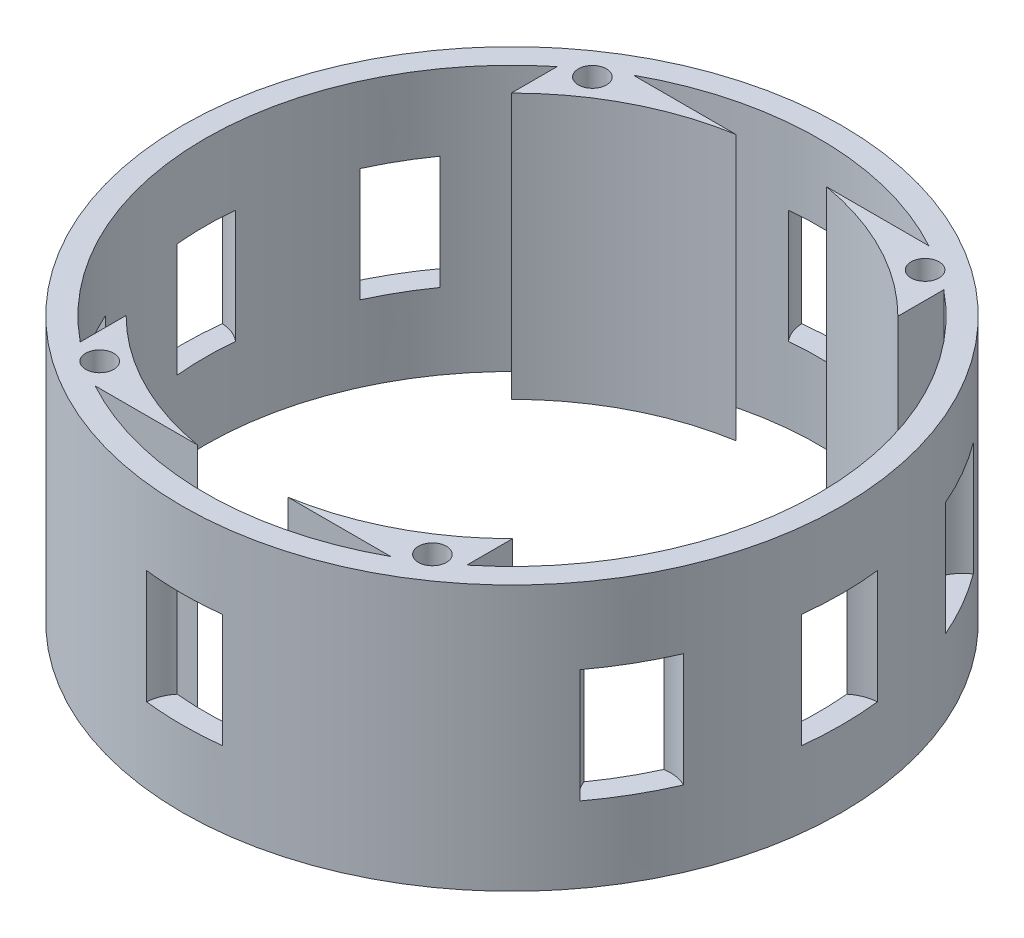
SolidWorks part; units mm, degrees
ref_plane "Front Plane" through (0, 0, 0) normal (0, 0, 1) x (1, 0, 0)
ref_plane "Top Plane" through (0, 0, 0) normal (0, 1, 0) x (1, 0, 0)
ref_plane "Right Plane" through (0, 0, 0) normal (1, 0, 0) x (0, 0, -1)
sketch "Sketch1" plane through (0, 0, 0) normal (0, 1, 0) x (1, 0, 0)
  line L0 (-25.5, 31.4643) -> (-25.5, 25.4116)
  line L5 (-25.5, 35.5) -> (25.5, -35.5) construction
  line L6 (-25.5, -35.5) -> (25.5, 35.5) construction
  line L7 (-19.4936, 35.5) -> (-5.9791, 35.5)
  line L8 (5.9791, 35.5) -> (19.4936, 35.5)
  line L9 (-25.5, -25.4116) -> (-25.5, -31.4643)
  line L10 (5.9791, -35.5) -> (19.4936, -35.5)
  line L11 (25.5, 31.4643) -> (25.5, 25.4116)
  line L12 (25.5, -25.4116) -> (25.5, -31.4643)
  line L13 (-19.4936, -35.5) -> (-5.9791, -35.5)
  circle A0 centre (0, 0) radius 40.5
  circle A1 centre (0, 0) radius 43.5
  arc A2 (-25.5, -25.4116) -> (-5.9791, -35.5) centre (0, 0) ccw
  arc A3 (25.5, 25.4116) -> (5.9791, 35.5) centre (0, 0) ccw
  arc A4 (5.9791, -35.5) -> (25.5, -25.4116) centre (0, 0) ccw
  arc A5 (-5.9791, 35.5) -> (-25.5, 25.4116) centre (0, 0) ccw
  dimension "D1" = 81
  dimension "D2" = 87
  dimension "D5" = 72
  dimension "D3" = 71
  dimension "D4" = 51
extrude "Boss-Extrude1" add sketch "Sketch1" along normal blind 35 contours A1 A0 | A2 L9 A0 L13 | A4 L10 A0 L12 | A3 L11 A0 L8 | A5 L7 A0 L0
sketch "Sketch2" plane through (0, 35, 0) normal (0, 1, 0) x (1, 0, 0)
  line L1 (-25, 35) -> (25, 35)
  line L2 (-25, 35) -> (-25, -35)
  line L3 (-25, -35) -> (25, -35)
  line L4 (25, 35) -> (25, -35)
  line L5 (-25, 35) -> (25, -35) construction
  line L6 (-25, -35) -> (25, 35) construction
  circle A0 centre (-22, 32.6064) radius 1.85
  circle A1 centre (22, 32.5) radius 1.85
  circle A2 centre (22, -32.5) radius 1.85
  circle A3 centre (-22, -32.3936) radius 1.85
  point P0 (0, 0)
  dimension "D7" = 3.7
  dimension "D1" = 70
  dimension "D2" = 50
  dimension "D3" = 65
  dimension "D4" = 65
  dimension "D5" = 44
  dimension "D6" = 44
  dimension "D8" = 3
  dimension "D9" = 3
  dimension "D10" = 2.6064
  dimension "D11" = 2.5
extrude "Cut-Extrude1" cut sketch "Sketch2" against normal blind 15 contours A0 | A1 | A2 | A3
sketch "Sketch3" plane through (0, 0, 0) normal (0, 0, 1) x (1, 0, 0)
  line L0 (0, -2.1211) -> (0, 39.6886) construction
  line L1 (-43.5, 17.5) -> (43.5, 17.5) construction
  line L2 (-43.5, 35) -> (-43.5, 0) construction
  line L3 (43.5, 0) -> (43.5, 35) construction
sketch "Sketch5" plane through (0, 0, 0) normal (0, 1, 0) x (1, 0, 0)
  circle A0 centre (0, 0) radius 43.5 construction
  arc A1 (19.4936, 35.5) -> (-19.4936, 35.5) centre (0, 0) ccw construction
  arc A2 (4.9917, 43.2126) -> (-4.9917, 43.2126) centre (0, 0) ccw
  arc A3 (3.8552, 40.3161) -> (-3.8552, 40.3161) centre (0, 0) ccw
  arc A4 (3.8552, 40.3161) -> (4.9917, 43.2126) centre (0, 43.5) ccw
  arc A5 (-4.9917, 43.2126) -> (-3.8552, 40.3161) centre (0, 43.5) ccw
  arc A10 (36.8424, 16.8193) -> (32.9871, 23.4968) centre (0, 0) ccw
  arc A11 (34.9274, 25.9293) -> (32.9871, 23.4968) centre (37.6721, 21.75) ccw
  arc A12 (39.9191, 17.2834) -> (34.9274, 25.9293) centre (0, 0) ccw
  arc A13 (36.8424, 16.8193) -> (39.9191, 17.2834) centre (37.6721, 21.75) ccw
  arc A14 (40.3161, -3.8552) -> (40.3161, 3.8552) centre (0, 0) ccw
  arc A15 (43.2126, 4.9917) -> (40.3161, 3.8552) centre (43.5, 0) ccw
  arc A16 (43.2126, -4.9917) -> (43.2126, 4.9917) centre (0, 0) ccw
  arc A17 (40.3161, -3.8552) -> (43.2126, -4.9917) centre (43.5, 0) ccw
  arc A18 (32.9871, -23.4968) -> (36.8424, -16.8193) centre (0, 0) ccw
  arc A19 (39.9191, -17.2834) -> (36.8424, -16.8193) centre (37.6721, -21.75) ccw
  arc A20 (34.9274, -25.9293) -> (39.9191, -17.2834) centre (0, 0) ccw
  arc A21 (32.9871, -23.4968) -> (34.9274, -25.9293) centre (37.6721, -21.75) ccw
  arc A26 (-3.8552, -40.3161) -> (3.8552, -40.3161) centre (0, 0) ccw
  arc A27 (4.9917, -43.2126) -> (3.8552, -40.3161) centre (0, -43.5) ccw
  arc A28 (-4.9917, -43.2126) -> (4.9917, -43.2126) centre (0, 0) ccw
  arc A29 (-3.8552, -40.3161) -> (-4.9917, -43.2126) centre (0, -43.5) ccw
  arc A34 (-36.8424, -16.8193) -> (-32.9871, -23.4968) centre (0, 0) ccw
  arc A35 (-34.9274, -25.9293) -> (-32.9871, -23.4968) centre (-37.6721, -21.75) ccw
  arc A36 (-39.9191, -17.2834) -> (-34.9274, -25.9293) centre (0, 0) ccw
  arc A37 (-36.8424, -16.8193) -> (-39.9191, -17.2834) centre (-37.6721, -21.75) ccw
  arc A38 (-40.3161, 3.8552) -> (-40.3161, -3.8552) centre (0, 0) ccw
  arc A39 (-43.2126, -4.9917) -> (-40.3161, -3.8552) centre (-43.5, 0) ccw
  arc A40 (-43.2126, 4.9917) -> (-43.2126, -4.9917) centre (0, 0) ccw
  arc A41 (-40.3161, 3.8552) -> (-43.2126, 4.9917) centre (-43.5, 0) ccw
  arc A42 (-32.9871, 23.4968) -> (-36.8424, 16.8193) centre (0, 0) ccw
  arc A43 (-39.9191, 17.2834) -> (-36.8424, 16.8193) centre (-37.6721, 21.75) ccw
  arc A44 (-34.9274, 25.9293) -> (-39.9191, 17.2834) centre (0, 0) ccw
  arc A45 (-32.9871, 23.4968) -> (-34.9274, 25.9293) centre (-37.6721, 21.75) ccw
  arc A50 (25.9293, -34.9274) -> (23.4968, -32.9871) centre (21.75, -37.6721) ccw [skipped]
  arc A51 (17.2834, -39.9191) -> (25.9293, -34.9274) centre (0, 0) ccw [skipped]
  arc A52 (16.8193, -36.8424) -> (23.4968, -32.9871) centre (0, 0) ccw [skipped]
  arc A53 (16.8193, -36.8424) -> (17.2834, -39.9191) centre (21.75, -37.6721) ccw [skipped]
  arc A54 (-17.2834, -39.9191) -> (-16.8193, -36.8424) centre (-21.75, -37.6721) ccw [skipped]
  arc A55 (-23.4968, -32.9871) -> (-25.9293, -34.9274) centre (-21.75, -37.6721) ccw [skipped]
  arc A56 (17.2834, 39.9191) -> (16.8193, 36.8424) centre (21.75, 37.6721) ccw [skipped]
  arc A57 (23.4968, 32.9871) -> (16.8193, 36.8424) centre (0, 0) ccw [skipped]
  arc A58 (25.9293, 34.9274) -> (17.2834, 39.9191) centre (0, 0) ccw [skipped]
  arc A59 (23.4968, 32.9871) -> (25.9293, 34.9274) centre (21.75, 37.6721) ccw [skipped]
  arc A60 (-16.8193, 36.8424) -> (-23.4968, 32.9871) centre (0, 0) ccw [skipped]
  arc A61 (-17.2834, 39.9191) -> (-25.9293, 34.9274) centre (0, 0) ccw [skipped]
  arc A62 (-16.8193, 36.8424) -> (-17.2834, 39.9191) centre (-21.75, 37.6721) ccw [skipped]
  arc A63 (-25.9293, 34.9274) -> (-23.4968, 32.9871) centre (-21.75, 37.6721) ccw [skipped]
  arc A64 (-25.9293, -34.9274) -> (-17.2834, -39.9191) centre (0, 0) ccw [skipped]
  arc A65 (-23.4968, -32.9871) -> (-16.8193, -36.8424) centre (0, 0) ccw [skipped]
  point P68 (0, 0)
  dimension "D1" = 10
  dimension "D2" = 12
ref_plane "Plane2" through (0, 17.5, 0) normal (0, 1, 0) x (1, 0, 0)
sketch "Sketch6" plane through (0, 17.5, 0) normal (0, 1, 0) x (1, 0, 0)
  arc A0 (-40.3161, 3.8552) -> (-43.2126, 4.9917) centre (-43.5, 0) ccw construction
  arc A1 (-43.2126, 4.9917) -> (-43.2126, -4.9917) centre (0, 0) ccw construction
  arc A2 (-40.3161, 3.8552) -> (-40.3161, -3.8552) centre (0, 0) ccw construction
  arc A3 (-43.2126, -4.9917) -> (-40.3161, -3.8552) centre (-43.5, 0) ccw construction
  arc A4 (-39.9191, -17.2834) -> (-34.9274, -25.9293) centre (0, 0) ccw construction
  arc A5 (-36.8424, -16.8193) -> (-32.9871, -23.4968) centre (0, 0) ccw construction
  arc A6 (-34.9274, -25.9293) -> (-32.9871, -23.4968) centre (-37.6721, -21.75) ccw construction
  arc A7 (-36.8424, -16.8193) -> (-39.9191, -17.2834) centre (-37.6721, -21.75) ccw construction
  arc A8 (4.9917, -43.2126) -> (3.8552, -40.3161) centre (0, -43.5) ccw construction
  arc A9 (-4.9917, -43.2126) -> (4.9917, -43.2126) centre (0, 0) ccw construction
  arc A10 (-3.8552, -40.3161) -> (3.8552, -40.3161) centre (0, 0) ccw construction
  arc A11 (-3.8552, -40.3161) -> (-4.9917, -43.2126) centre (0, -43.5) ccw construction
  arc A12 (34.9274, -25.9293) -> (39.9191, -17.2834) centre (0, 0) ccw construction
  arc A13 (32.9871, -23.4968) -> (36.8424, -16.8193) centre (0, 0) ccw construction
  arc A14 (39.9191, -17.2834) -> (36.8424, -16.8193) centre (37.6721, -21.75) ccw construction
  arc A15 (32.9871, -23.4968) -> (34.9274, -25.9293) centre (37.6721, -21.75) ccw construction
  arc A16 (40.3161, -3.8552) -> (40.3161, 3.8552) centre (0, 0) ccw construction
  arc A17 (43.2126, -4.9917) -> (43.2126, 4.9917) centre (0, 0) ccw construction
  arc A18 (43.2126, 4.9917) -> (40.3161, 3.8552) centre (43.5, 0) ccw construction
  arc A19 (40.3161, -3.8552) -> (43.2126, -4.9917) centre (43.5, 0) ccw construction
  arc A20 (39.9191, 17.2834) -> (34.9274, 25.9293) centre (0, 0) ccw construction
  arc A21 (34.9274, 25.9293) -> (32.9871, 23.4968) centre (37.6721, 21.75) ccw construction
  arc A22 (36.8424, 16.8193) -> (32.9871, 23.4968) centre (0, 0) ccw construction
  arc A23 (36.8424, 16.8193) -> (39.9191, 17.2834) centre (37.6721, 21.75) ccw construction
  arc A24 (3.8552, 40.3161) -> (-3.8552, 40.3161) centre (0, 0) ccw construction
  arc A25 (-4.9917, 43.2126) -> (-3.8552, 40.3161) centre (0, 43.5) ccw construction
  arc A26 (4.9917, 43.2126) -> (-4.9917, 43.2126) centre (0, 0) ccw construction
  arc A27 (3.8552, 40.3161) -> (4.9917, 43.2126) centre (0, 43.5) ccw construction
  arc A28 (-34.9274, 25.9293) -> (-39.9191, 17.2834) centre (0, 0) ccw construction
  arc A29 (-39.9191, 17.2834) -> (-36.8424, 16.8193) centre (-37.6721, 21.75) ccw construction
  arc A30 (-32.9871, 23.4968) -> (-36.8424, 16.8193) centre (0, 0) ccw construction
  arc A31 (-32.9871, 23.4968) -> (-34.9274, 25.9293) centre (-37.6721, 21.75) ccw construction
  arc A32 (-40.3161, 3.8552) -> (-43.2126, 4.9917) centre (-43.5, 0) ccw
  arc A33 (-43.2126, 4.9917) -> (-43.2126, -4.9917) centre (0, 0) ccw
  arc A34 (-40.3161, 3.8552) -> (-40.3161, -3.8552) centre (0, 0) ccw
  arc A35 (-43.2126, -4.9917) -> (-40.3161, -3.8552) centre (-43.5, 0) ccw
  arc A36 (-39.9191, -17.2834) -> (-34.9274, -25.9293) centre (0, 0) ccw
  arc A37 (-36.8424, -16.8193) -> (-32.9871, -23.4968) centre (0, 0) ccw
  arc A38 (-34.9274, -25.9293) -> (-32.9871, -23.4968) centre (-37.6721, -21.75) ccw
  arc A39 (-36.8424, -16.8193) -> (-39.9191, -17.2834) centre (-37.6721, -21.75) ccw
  arc A40 (4.9917, -43.2126) -> (3.8552, -40.3161) centre (0, -43.5) ccw
  arc A41 (-4.9917, -43.2126) -> (4.9917, -43.2126) centre (0, 0) ccw
  arc A42 (-3.8552, -40.3161) -> (3.8552, -40.3161) centre (0, 0) ccw
  arc A43 (-3.8552, -40.3161) -> (-4.9917, -43.2126) centre (0, -43.5) ccw
  arc A44 (34.9274, -25.9293) -> (39.9191, -17.2834) centre (0, 0) ccw
  arc A45 (32.9871, -23.4968) -> (36.8424, -16.8193) centre (0, 0) ccw
  arc A46 (39.9191, -17.2834) -> (36.8424, -16.8193) centre (37.6721, -21.75) ccw
  arc A47 (32.9871, -23.4968) -> (34.9274, -25.9293) centre (37.6721, -21.75) ccw
  arc A48 (40.3161, -3.8552) -> (40.3161, 3.8552) centre (0, 0) ccw
  arc A49 (43.2126, -4.9917) -> (43.2126, 4.9917) centre (0, 0) ccw
  arc A50 (43.2126, 4.9917) -> (40.3161, 3.8552) centre (43.5, 0) ccw
  arc A51 (40.3161, -3.8552) -> (43.2126, -4.9917) centre (43.5, 0) ccw
  arc A52 (39.9191, 17.2834) -> (34.9274, 25.9293) centre (0, 0) ccw
  arc A53 (34.9274, 25.9293) -> (32.9871, 23.4968) centre (37.6721, 21.75) ccw
  arc A54 (36.8424, 16.8193) -> (32.9871, 23.4968) centre (0, 0) ccw
  arc A55 (36.8424, 16.8193) -> (39.9191, 17.2834) centre (37.6721, 21.75) ccw
  arc A56 (3.8552, 40.3161) -> (-3.8552, 40.3161) centre (0, 0) ccw
  arc A57 (-4.9917, 43.2126) -> (-3.8552, 40.3161) centre (0, 43.5) ccw
  arc A58 (4.9917, 43.2126) -> (-4.9917, 43.2126) centre (0, 0) ccw
  arc A59 (3.8552, 40.3161) -> (4.9917, 43.2126) centre (0, 43.5) ccw
  arc A60 (-34.9274, 25.9293) -> (-39.9191, 17.2834) centre (0, 0) ccw
  arc A61 (-39.9191, 17.2834) -> (-36.8424, 16.8193) centre (-37.6721, 21.75) ccw
  arc A62 (-32.9871, 23.4968) -> (-36.8424, 16.8193) centre (0, 0) ccw
  arc A63 (-32.9871, 23.4968) -> (-34.9274, 25.9293) centre (-37.6721, 21.75) ccw
extrude "Cut-Extrude3" cut sketch "Sketch6" against normal blind 7.5 and the other way blind 7.5
sketch "Sketch7" plane through (0, 35, 0) normal (0, 1, 0) x (1, 0, 0)
  circle A0 centre (0, 0) radius 43.5 construction
  circle A1 centre (0, 0) radius 43.5
  circle A2 centre (0, 0) radius 40.5
